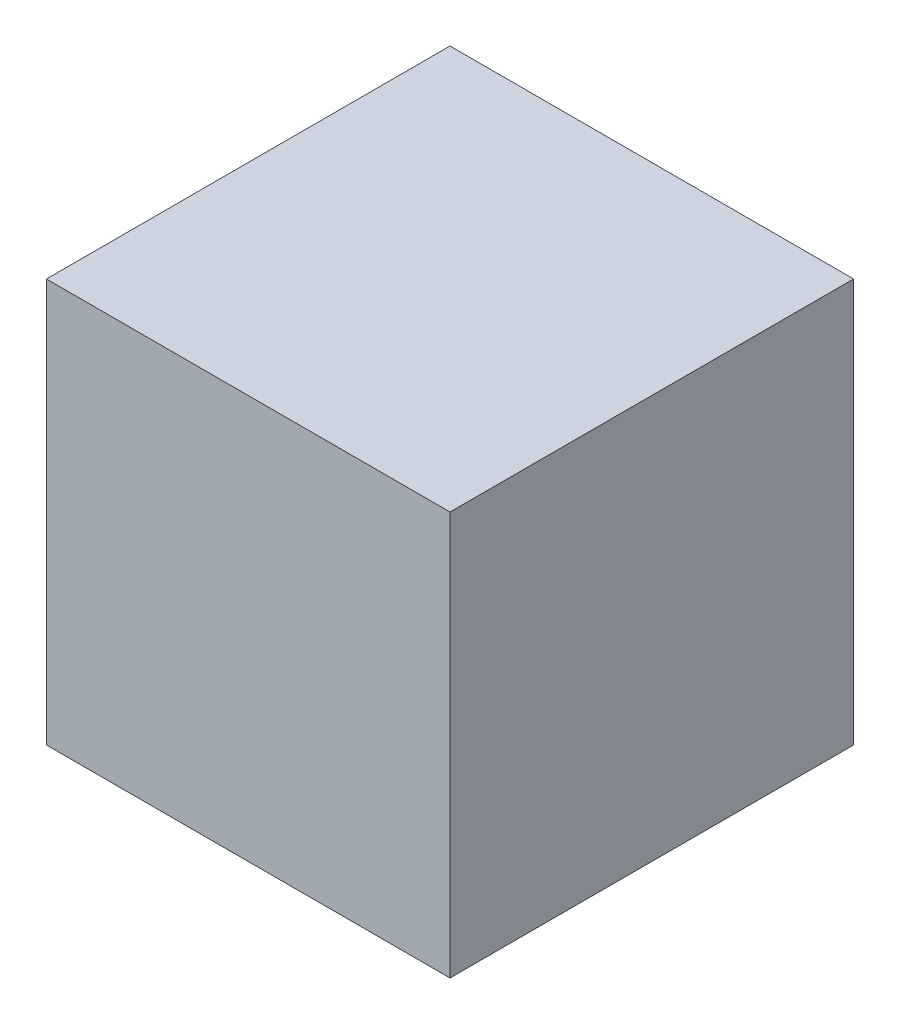
SolidWorks part; units mm, degrees
ref_plane "Front Plane" through (0, 0, 0) normal (0, 0, 1) x (1, 0, 0)
ref_plane "Top Plane" through (0, 0, 0) normal (0, 1, 0) x (1, 0, 0)
ref_plane "Right Plane" through (0, 0, 0) normal (1, 0, 0) x (0, 0, -1)
sketch "Sketch4" plane through (0, 0, 0) normal (0, 0, 1) x (1, 0, 0)
  line L1 (30.5, -30.5) -> (-30.5, -30.5)
  line L2 (30.5, -30.5) -> (30.5, 30.5)
  line L3 (30.5, 30.5) -> (-30.5, 30.5)
  line L4 (-30.5, -30.5) -> (-30.5, 30.5)
  point P0 (0, 0)
  dimension "D1" = 61
  dimension "D2" = 61
extrude "Boss-Extrude4" add sketch "Sketch4" along normal blind 61
